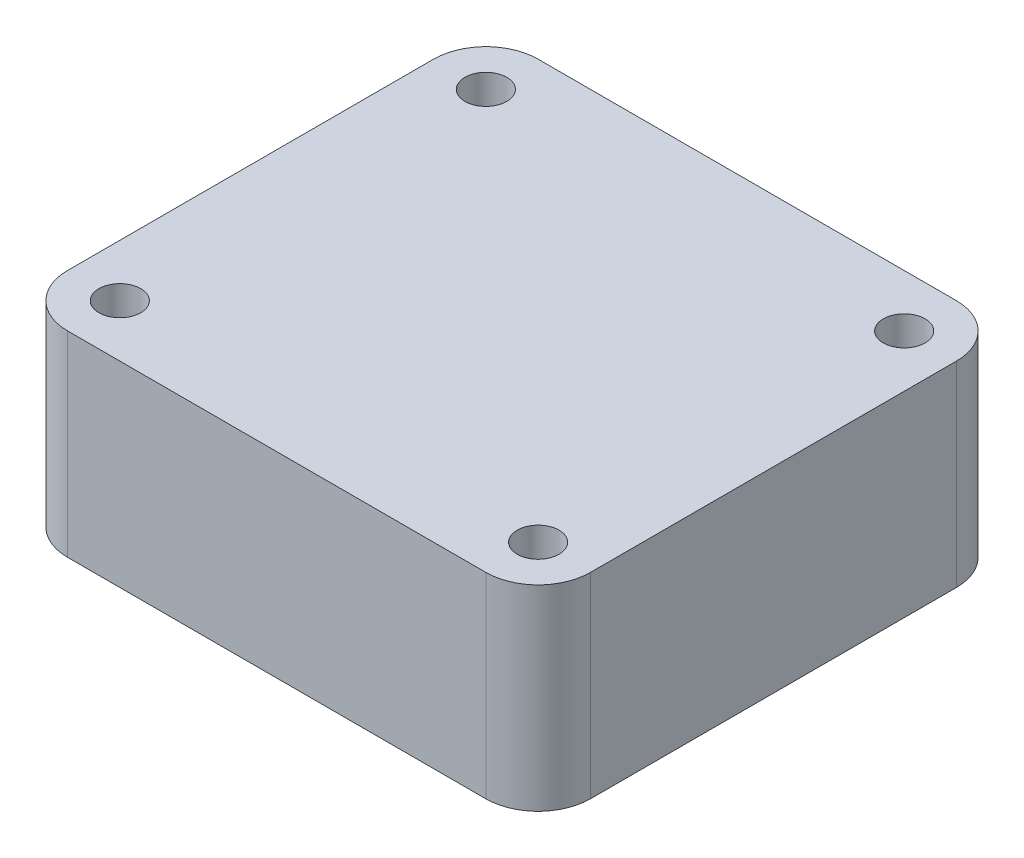
SolidWorks part; units mm, degrees
ref_plane "Front Plane" through (0, 0, 0) normal (0, 0, 1) x (1, 0, 0)
ref_plane "Top Plane" through (0, 0, 0) normal (0, 1, 0) x (1, 0, 0)
ref_plane "Right Plane" through (0, 0, 0) normal (1, 0, 0) x (0, 0, -1)
sketch "Sketch1" plane through (0, 0, 0) normal (0, 1, 0) x (1, 0, 0)
  line L1 (-16, -18) -> (16, -18)
  line L2 (-20, -14) -> (-20, 14)
  line L3 (-16, 18) -> (16, 18)
  line L4 (20, -14) -> (20, 14)
  line L5 (-20, -18) -> (20, 18) construction
  line L6 (-20, 18) -> (20, -18) construction
  line L7 (-16, -14) -> (16, -14) construction
  line L8 (-16, -14) -> (-16, 14) construction
  line L9 (-16, 14) -> (16, 14) construction
  line L10 (16, -14) -> (16, 14) construction
  line L11 (-16, -14) -> (16, 14) construction
  line L12 (-16, 14) -> (16, -14) construction
  arc A0 (-16, -18) -> (-20, -14) centre (-16, -14) cw
  arc A1 (16, -18) -> (20, -14) centre (16, -14) ccw
  arc A2 (16, 18) -> (20, 14) centre (16, 14) cw
  arc A3 (-16, 18) -> (-20, 14) centre (-16, 14) ccw
  circle A8 centre (16, 14) radius 1.6
  circle A9 centre (-16, 14) radius 1.6
  circle A10 centre (-16, -14) radius 1.6
  circle A11 centre (16, -14) radius 1.6
  point P0 (0, 0)
  point P18 (0, 0)
  dimension "D3" = 4
  dimension "D4" = 3.2
  dimension "D1" = 40
  dimension "D2" = 36
  dimension "D5" = 28
  dimension "D6" = 32
extrude "Boss-Extrude1" add sketch "Sketch1" along normal blind 15
